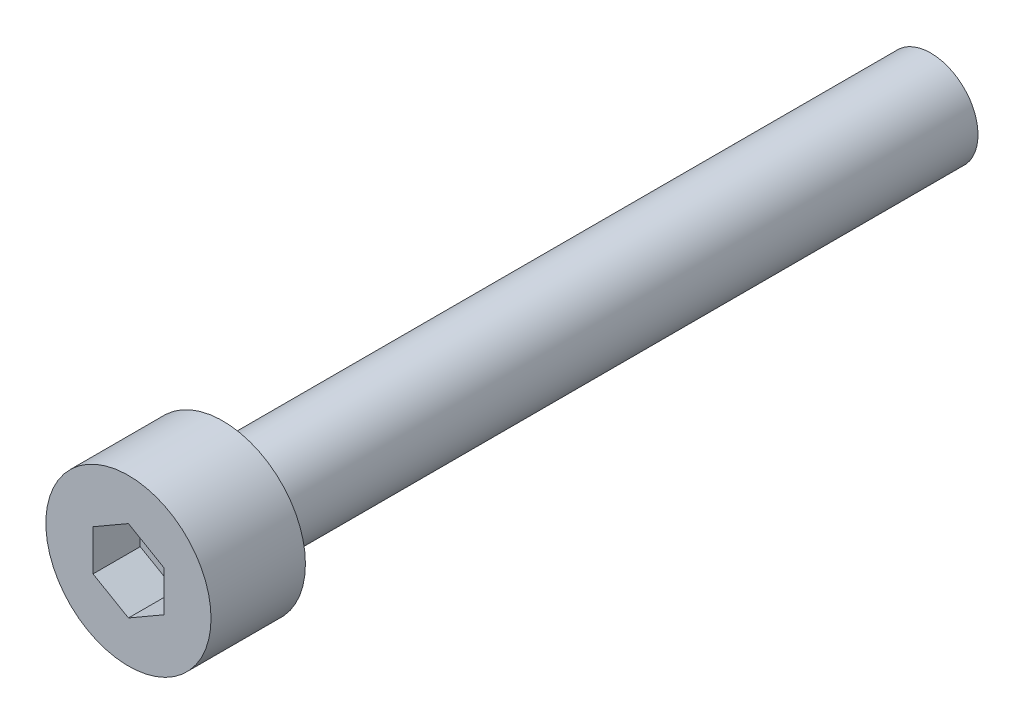
SolidWorks part; units mm, degrees
ref_plane "Front Plane" through (0, 0, 0) normal (0, 0, 1) x (1, 0, 0)
ref_plane "Top Plane" through (0, 0, 0) normal (0, 1, 0) x (1, 0, 0)
ref_plane "Right Plane" through (0, 0, 0) normal (1, 0, 0) x (0, 0, -1)
sketch "Sketch1" plane through (0, 0, 0) normal (0, 0, 1) x (1, 0, 0)
  circle A0 centre (0, 0) radius 3.5
extrude "Boss-Extrude1" add sketch "Sketch1" along normal blind 4
sketch "Sketch2" plane through (0, 0, 4) normal (0, 0, 1) x (1, 0, 0)
  line L1 (0, -1.7321) -> (1.5, -0.866)
  line L2 (1.5, -0.866) -> (1.5, 0.866)
  line L3 (1.5, 0.866) -> (0, 1.7321)
  line L4 (0, 1.7321) -> (-1.5, 0.866)
  line L5 (-1.5, 0.866) -> (-1.5, -0.866)
  line L6 (-1.5, -0.866) -> (0, -1.7321)
  circle A0 centre (0, 0) radius 1.5 construction
  dimension "D1" = 3
extrude "Cut-Extrude1" cut sketch "Sketch2" against normal blind 2
sketch "Sketch3" plane through (0, 0, 0) normal (0, 0, -1) x (-1, 0, 0)
  circle A0 centre (0, 0) radius 2
extrude "Boss-Extrude2" add sketch "Sketch3" along normal blind 30
